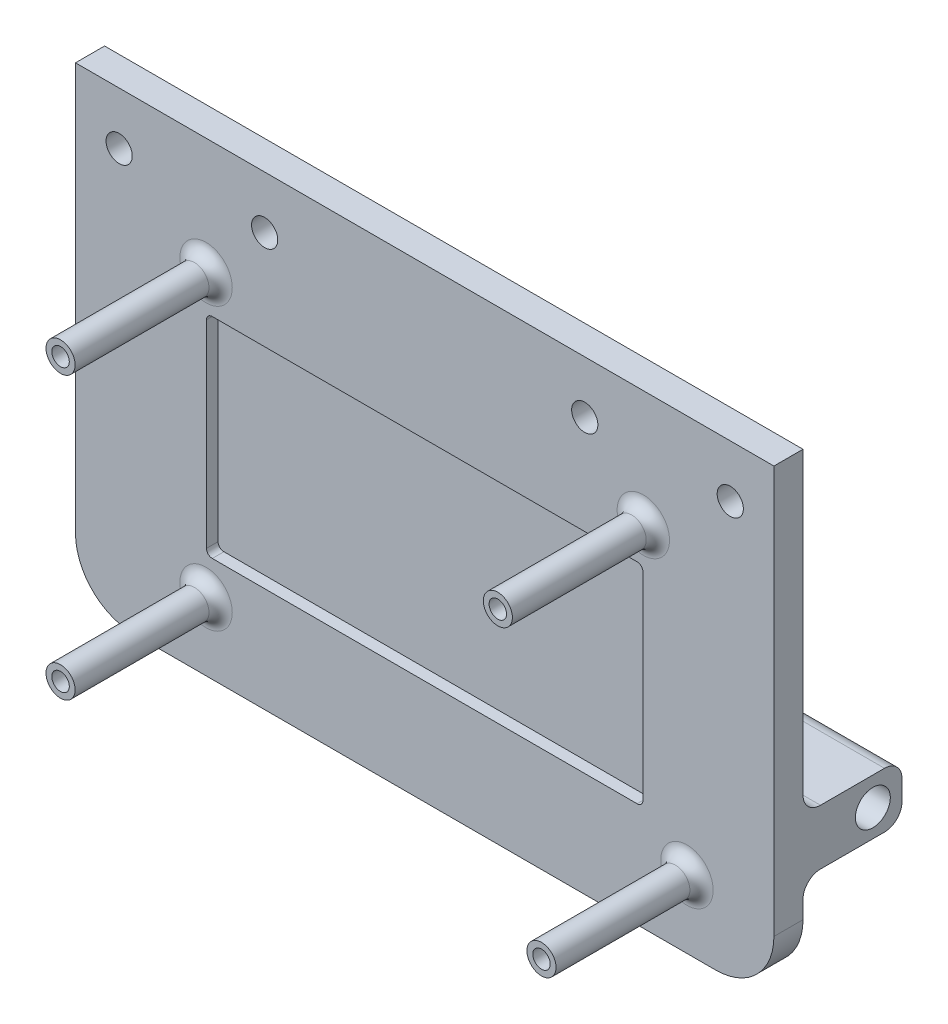
SolidWorks part; units mm, degrees
material "Cast Alloy Steel"
ref_plane "Front Plane" through (0, 0, 0) normal (0, 0, 1) x (1, 0, 0)
ref_plane "Top Plane" through (0, 0, 0) normal (0, 1, 0) x (1, 0, 0)
ref_plane "Right Plane" through (0, 0, 0) normal (1, 0, 0) x (0, 0, -1)
sketch "Sketch1" plane through (0, 0, 0) normal (0, 0, 1) x (1, 0, 0)
  line L0 (60, 0) -> (-60, 0)
  line L1 (-60, 0) -> (-60, -80)
  line L2 (-60, -80) -> (60, -80)
  line L3 (0, 0) -> (0, -80) construction
  line L4 (60, 0) -> (60, -80)
  dimension "D1" = 80
  dimension "D2" = 60
extrude "Boss-Extrude1" add sketch "Sketch1" along normal mid plane 5
fillet "Fillet1" radius 10 2 edges at (60, -80, 0) (-60, -80, 0)
sketch "Sketch2" plane through (0, 0, 2.5) normal (0, 0, 1) x (1, 0, 0)
  line L0 (60, 0) -> (-60, 0) construction
  line L1 (0, 0) -> (0, -17.0614) construction
  circle A0 centre (-52.5, -9) radius 2.25
  circle A1 centre (-27.5, -9) radius 2.25
  circle A2 centre (27.5, -9) radius 2.25
  circle A3 centre (52.5, -9) radius 2.25
  dimension "D1" = 4.5
  dimension "D2" = 25
  dimension "D3" = 9
  dimension "D4" = 27.5
extrude "Cut-Extrude1" cut sketch "Sketch2" against normal through all
sketch "Sketch3" plane through (0, 0, 2.5) normal (0, 0, 1) x (1, 0, 0)
  line L0 (-37.565, -20) -> (-37.565, -68.34) construction
  line L1 (-37.565, -68.34) -> (45.065, -68.34) construction
  line L2 (37.565, -20) -> (45.065, -68.34) construction
  line L3 (37.565, -20) -> (-37.565, -20) construction
  circle A0 centre (-37.565, -20) radius 2.5
  circle A1 centre (37.565, -20) radius 2.5
  circle A2 centre (-37.565, -68.34) radius 2.5
  circle A3 centre (45.065, -68.34) radius 2.5
  circle A4 centre (-37.565, -20) radius 1.5
  circle A5 centre (37.565, -20) radius 1.5
  circle A6 centre (45.065, -68.34) radius 1.5
  circle A7 centre (-37.565, -68.34) radius 1.5
  point P2 (0, -20)
  dimension "D5" = 5
  dimension "D6" = 3
  dimension "D1" = 75.13
  dimension "D2" = 48.34
  dimension "D3" = 82.63
  dimension "D4" = 20
extrude "Boss-Extrude2" add sketch "Sketch3" along normal blind 25
fillet "Fillet2" radius 2 4 edges at (40.065, -20, 2.5) (47.565, -68.34, 2.5) (-35.065, -68.34, 2.5) (-35.065, -20, 2.5)
sketch "Sketch4" plane through (0, 0, 2.5) normal (0, 0, 1) x (1, 0, 0)
  line L1 (-36.5, -62) -> (36.5, -62)
  line L2 (-37.5, -61) -> (-37.5, -27)
  line L3 (-36.5, -26) -> (36.5, -26)
  line L4 (37.5, -61) -> (37.5, -27)
  line L5 (-37.5, -62) -> (37.5, -26) construction
  line L6 (-37.5, -26) -> (37.5, -62) construction
  arc A0 (36.5, -62) -> (37.5, -61) centre (36.5, -61) ccw
  arc A1 (36.5, -26) -> (37.5, -27) centre (36.5, -27) cw
  arc A2 (-36.5, -62) -> (-37.5, -61) centre (-36.5, -61) cw
  arc A3 (-37.5, -27) -> (-36.5, -26) centre (-36.5, -27) cw
  point P0 (0, -44)
  dimension "D4" = 1
  dimension "D1" = 75
  dimension "D2" = 36
  dimension "D3" = 44
extrude "Cut-Extrude2" cut sketch "Sketch4" against normal blind 2
ref_plane "Plane1" through (60, -70, 2.5) normal (0, 1, 0) x (1, 0, 0)
sketch "Sketch6" plane through (60, 0, 0) normal (1, 0, 0) x (0, 0, -1)
  line L0 (2.5, -63.9715) -> (19.5, -63.9715)
  line L2 (19.5, -63.9715) -> (19.5, -54.4715)
  line L3 (19.5, -54.4715) -> (2.5, -54.4715)
  line L4 (2.5, -54.4715) -> (2.5, -63.9715)
  line L5 (2.5, -70) -> (2.5, 0) construction
  circle A0 centre (14.5, -59.3208) radius 3
  dimension "D1" = 6
  dimension "D2" = 12
  dimension "D3" = 17
  dimension "D4" = 9.5
extrude "Boss-Extrude3" add sketch "Sketch6" against normal blind 30
fillet "Fillet3" radius 3 4 edges at (45, -54.4715, -19.5) (45, -63.9715, -19.5)
mirror "Mirror1" about plane through (0, 0, 0) normal (1, 0, 0) of "Fillet3", "Boss-Extrude3"
